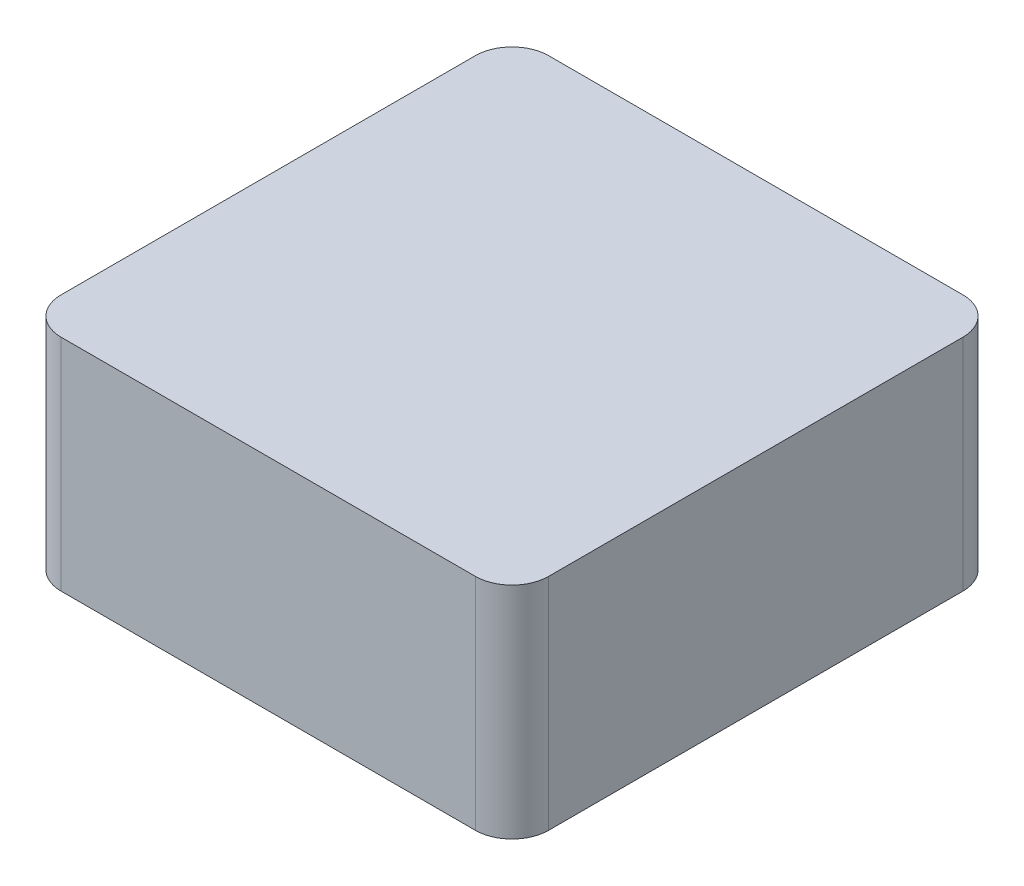
SolidWorks part; units mm, degrees
ref_plane "Front Plane" through (0, 0, 0) normal (0, 0, 1) x (1, 0, 0)
ref_plane "Top Plane" through (0, 0, 0) normal (0, 1, 0) x (1, 0, 0)
ref_plane "Right Plane" through (0, 0, 0) normal (1, 0, 0) x (0, 0, -1)
sketch "Sketch1" plane through (0, 0, 0) normal (0, 1, 0) x (1, 0, 0)
  line L1 (-3.325, -3.325) -> (3.325, -3.325)
  line L2 (-3.325, -3.325) -> (-3.325, 3.325)
  line L3 (-3.325, 3.325) -> (3.325, 3.325)
  line L4 (3.325, -3.325) -> (3.325, 3.325)
  line L5 (-3.325, -3.325) -> (3.325, 3.325) construction
  line L6 (-3.325, 3.325) -> (3.325, -3.325) construction
  point P0 (0, 0)
  dimension "D1" = 6.65
extrude "Boss-Extrude1" add sketch "Sketch1" along normal blind 3
fillet "Fillet1" radius 0.5 4 edges at (3.325, 1.5, -3.325) (-3.325, 1.5, -3.325) (-3.325, 1.5, 3.325) (3.325, 1.5, 3.325)
